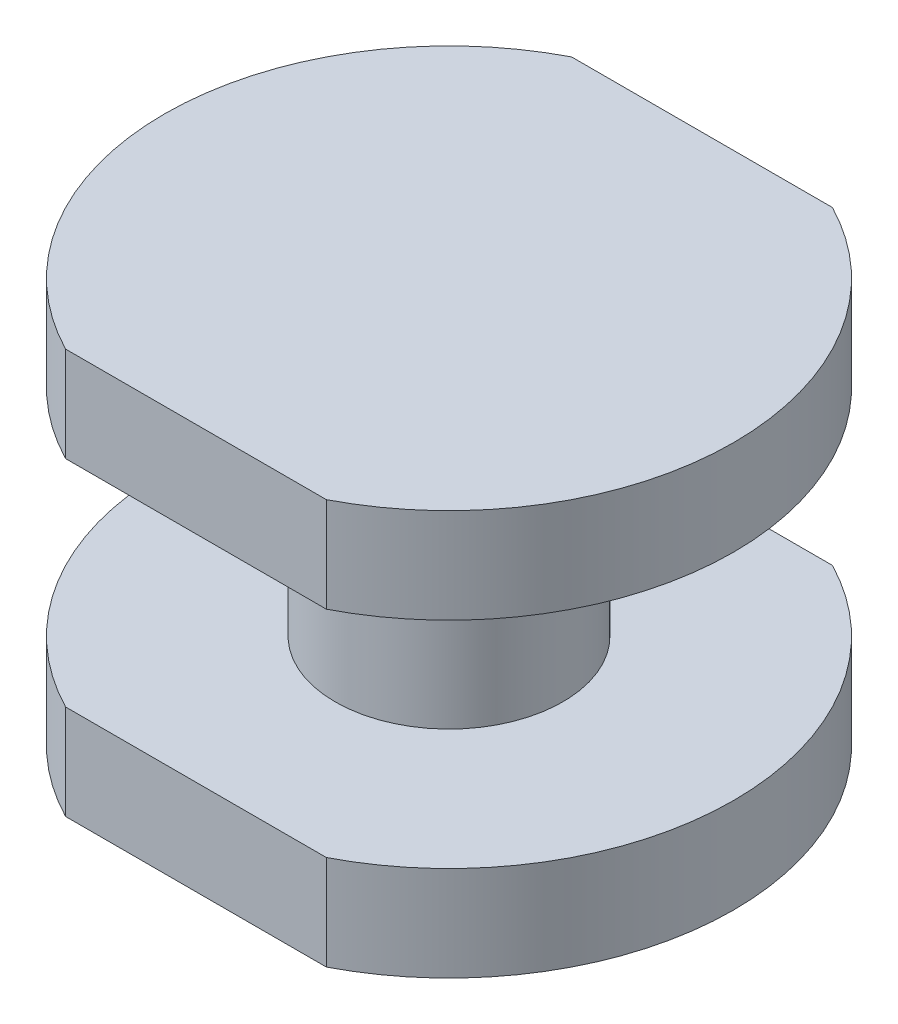
SolidWorks part; units mm, degrees
ref_plane "Front Plane" through (0, 0, 0) normal (0, 0, 1) x (1, 0, 0)
ref_plane "Top Plane" through (0, 0, 0) normal (0, 1, 0) x (1, 0, 0)
ref_plane "Right Plane" through (0, 0, 0) normal (1, 0, 0) x (0, 0, -1)
sketch "Sketch1" plane through (0, 0, 0) normal (0, 1, 0) x (1, 0, 0)
  line L1 (-1.0308, -2) -> (1.0308, -2)
  line L3 (-1.0308, 2) -> (1.0308, 2)
  arc A2 (1.0308, -2) -> (1.0308, 2) centre (0, 0) ccw
  arc A3 (-1.0308, 2) -> (-1.0308, -2) centre (0, 0) ccw
  point P9 (0, 2)
  dimension "D3" = 4.5
  dimension "D2" = 4
extrude "Boss-Extrude1" add sketch "Sketch1" along normal blind 0.75
sketch "Sketch2" plane through (0, 0.75, 0) normal (0, 1, 0) x (1, 0, 0)
  circle A0 centre (0, 0) radius 0.9
  dimension "D1" = 1.8
extrude "Boss-Extrude2" add sketch "Sketch2" along normal blind 1.7
sketch "Sketch3" plane through (0, 2.45, 0) normal (0, 1, 0) x (1, 0, 0)
  line L0 (-1.0308, 2) -> (1.0308, 2)
  line L5 (1.0308, 2) -> (-1.0308, 2) construction
  line L6 (-1.0308, -2) -> (1.0308, -2)
  line L7 (-1.0308, -2) -> (1.0308, -2) construction
  arc A0 (1.0308, -2) -> (1.0308, 2) centre (0, 0) ccw
  arc A1 (-1.0308, 2) -> (-1.0308, -2) centre (0, 0) ccw construction
  arc A2 (-1.0308, 2) -> (-1.0308, -2) centre (0, 0) ccw
extrude "Boss-Extrude3" add sketch "Sketch3" along normal blind 0.75
